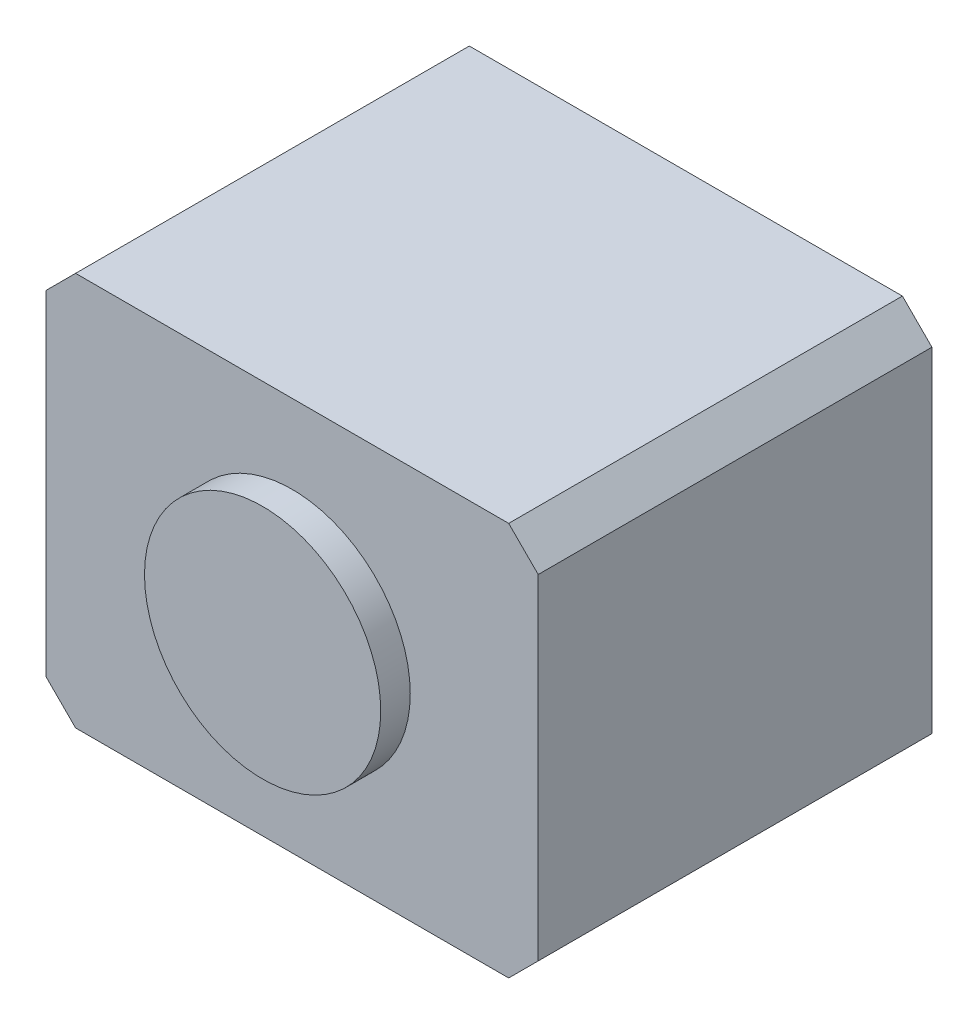
SolidWorks part; units mm, degrees
ref_plane "Front" through (0, 0, 0) normal (0, 0, 1) x (1, 0, 0)
ref_plane "Top" through (0, 0, 0) normal (0, 1, 0) x (1, 0, 0)
ref_plane "Right" through (0, 0, 0) normal (1, 0, 0) x (0, 0, -1)
sketch "Sketch2" plane through (0, 0, 0) normal (0, 0, 1) x (1, 0, 0)
  line L1 (-12.5, -10) -> (12.5, -10)
  line L2 (-12.5, -10) -> (-12.5, 10)
  line L3 (-12.5, 10) -> (12.5, 10)
  line L4 (12.5, -10) -> (12.5, 10)
  line L5 (-12.5, -10) -> (12.5, 10) construction
  line L6 (-12.5, 10) -> (12.5, -10) construction
  point P0 (0, 0)
  dimension "D1" = 20
  dimension "D2" = 25
extrude "Boss-Extrude1" add sketch "Sketch2" along normal blind 20
chamfer "Chamfer1" distance 1.5 angle 45 4 edges at (-12.5, 10, 10) (-12.5, -10, 10) (12.5, -10, 10) (12.5, 10, 10)
sketch "Sketch3" plane through (0, 0, 20) normal (0, 0, 1) x (1, 0, 0)
  circle A0 centre (0, 0) radius 6
  dimension "D1" = 12
extrude "Boss-Extrude2" add sketch "Sketch3" along normal blind 1.5
